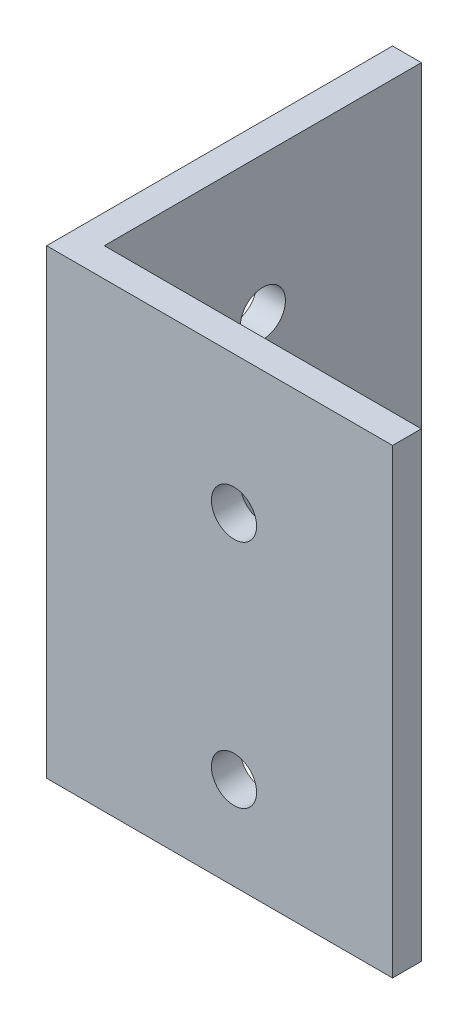
SolidWorks part; units mm, degrees
material "6061-T6 (SS)"
ref_plane "Front" through (0, 0, 0) normal (0, 0, 1) x (1, 0, 0)
ref_plane "Top" through (0, 0, 0) normal (0, 1, 0) x (1, 0, 0)
ref_plane "Right" through (0, 0, 0) normal (1, 0, 0) x (0, 0, -1)
sketch "Sketch1" plane through (0, 0, 0) normal (0, 1, 0) x (1, 0, 0)
  line L0 (0, 38.1) -> (0, 0)
  line L1 (0, 0) -> (38.1, 0)
  dimension "D1" = 38.1
extrude "Extrude-Thin1" add sketch "Sketch1" along normal mid plane 50.8 thin thin type one direction reverse wall 3.175
sketch "Sketch2" plane through (0, 0, -3.175) normal (0, 0, -1) x (-1, 0, 0)
  line L0 (-20.6375, 25.4) -> (-20.6375, -25.4) construction
  line L1 (-3.175, 25.4) -> (-38.1, 25.4) construction
  line L2 (-3.175, -25.4) -> (-38.1, -25.4) construction
  circle A0 centre (-20.6375, 10.2108) radius 2.4892
  circle A1 centre (-20.6375, -15.1892) radius 2.4892
  dimension "D1" = 4.9784
  dimension "D2" = 10.2108
  dimension "D3" = 25.4
extrude "Cut-Extrude1" cut sketch "Sketch2" against normal through all
ref_plane "Plane1" through (0, 0, 0) normal (-0.7071, 0, -0.7071) x (-0.7071, 0, 0.7071)
mirror "Mirror1" about plane through (0, 0, 0) normal (-0.7071, 0, -0.7071) of "Cut-Extrude1"
